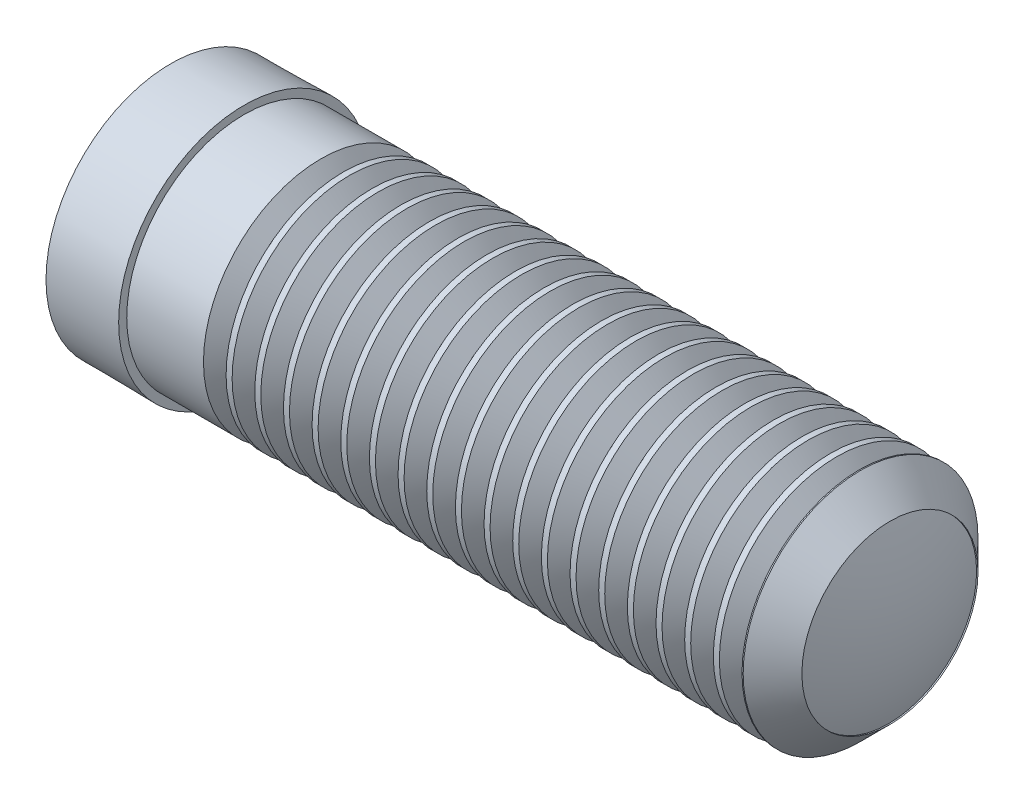
SolidWorks part; units mm, degrees
ref_plane "Front" through (0, 0, 0) normal (0, 0, 1) x (1, 0, 0)
ref_plane "Top" through (0, 0, 0) normal (0, 1, 0) x (1, 0, 0)
ref_plane "Right" through (0, 0, 0) normal (1, 0, 0) x (0, 0, -1)
sketch "BodySke" plane through (0, 0, 0) normal (0, 0, 1) x (1, 0, 0)
  line L0 (-8.7403, 0) -> (75.0119, 0) construction
  line L1 (0, 0) -> (0, 8.5)
  line L2 (0, 8.5) -> (5, 8.55)
  line L3 (5, 8.55) -> (5, 8)
  line L4 (5, 8) -> (47, 8)
  line L5 (47, 8) -> (49, 6)
  line L6 (49, 6) -> (48.906, 6)
  line L7 (0, 0) -> (50, 0)
  line L8 (11, 20.1179) -> (11, -6.4248) construction
  line L10 (13, 20.1179) -> (13, -6.4248) construction
  arc A0 (50, 0) -> (48.906, 6) centre (33, 0) ccw
  dimension "D1" = 45
  dimension "D2" = 0.573
  dimension "Head_rad" = 17
  dimension "Length" = 50
  dimension "Diameter" = 17
  dimension "Thread_dia" = 16
  dimension "Thread_len" = 39
  dimension "Thread_clr" = 6
  dimension "Head_dia" = 12
  dimension "Head_ht" = 1
  dimension "Advance" = 2
revolve "Body" add sketch "BodySke" angle 360 about L0
cosmetic thread "ThreadCosmetic" [suppressed] parameters "Length"=38, "Thread_minor"=13.797
sketch "ThdSchSke" plane through (0, 0, 0) normal (0, 0, 1) x (1, 0, 0)
  line L0 (11, 6.8985) -> (10.1937, 8.05)
  line L1 (11, 0) -> (11, 10.6732) construction
  line L2 (11, 6.8985) -> (11.8063, 8.05)
  line L3 (11.8063, 8.05) -> (10.1937, 8.05)
  line L4 (112.0749, 0) -> (123.8916, 0) construction
  line L8 (5, -8.55) -> (5, 8.55) construction
  dimension "D1" = 70
  dimension "Inset" = 6
  dimension "Thread_minor" = 13.797
  dimension "DieOD" = 16.1
revolve "ThreadSchematic" cut sketch "ThdSchSke" angle 360 about L4
pattern_linear "ThdSchPat" count 19 spacing 1.9527 along (1, 0, 0) of "ThreadSchematic"
ref_plane "Plane1" through (0, 8, 0) normal (0, 1, 0) x (-1, 0, 0)
sketch "Sketch3" plane through (0, 8, 0) normal (0, 1, 0) x (-1, 0, 0)
  line L0 (-5, 8.55) -> (-5, -8.55) construction
  line L1 (-56.0294, -13.2045) -> (-6, -13.2045)
  line L2 (-56.0294, -13.2045) -> (-56.0294, 13.5986)
  line L3 (-56.0294, 13.5986) -> (-6, 13.5986)
  line L4 (-6, -13.2045) -> (-6, 13.5986)
  dimension "D1" = 1
equation "' \"Diameter@BodySke\" = 20"
equation "' \"Thread_dia@BodySke\" = 16"
equation "' \"Advance@BodySke\" = 2"
equation "' \"Thread_clr@BodySke\" = 6"
equation "' \"Thread_len@BodySke\" = 39"
equation "' \"Head_dia@BodySke\" = 12"
equation "' \"Head_ht@BodySke\" = 4.3"
equation "' \"Length@BodySke\" = 120"
equation "' \"Thread_minor@ThreadCosmetic\"  = 13.797"
equation "' \"Diameter@BodySke\" = 5"
equation "' \"Thread_dia@BodySke\" = 5"
equation "' \"Advance@BodySke\" = 0.8"
equation "' \"Thread_clr@BodySke\" = 2.4"
equation "' \"Thread_len@BodySke\" = 15.6"
equation "' \"Head_dia@BodySke\" = 3.5"
equation "' \"Head_ht@BodySke\" = 1.5"
equation "' \"Length@BodySke\" = 40"
equation "' \"Thread_minor@ThreadCosmetic\"  = 4.11"
equation "\"Head_rad@BodySke\" = \"Diameter@BodySke\""
equation "\"Length@ThreadCosmetic\" = \"Thread_len@BodySke\" - \"Head_ht@BodySke\""
equation "\"Thread_minor@ThdSchSke\" = \"Thread_minor@ThreadCosmetic\" "
equation "\"DieOD@ThdSchSke\" =  \"Thread_dia@BodySke\" + 0.1"
equation "\"Inset@ThdSchSke\" = \"Thread_clr@BodySke\""
equation "\"Num_threads@ThdSchPat\" = int(  ( \"Thread_len@BodySke\" - \"Head_ht@BodySke\" -   (\"Thread_minor@ThdSchSke\" - \"Head_dia@BodySke\" ) / 2 * tan(45 * 0.0174533) ) / \"Advance@BodySke\" + 0.999 )"
equation "\"Advance@ThdSchPat\" = (  \"Thread_len@BodySke\"  - \"Head_ht@BodySke\"  - (\"Thread_minor@ThdSchSke\" - \"Head_dia@BodySke\" ) / 2 * tan(45 * 0.0174533)) /  (\"Num_threads@ThdSchPat\" ) 'relax it"
